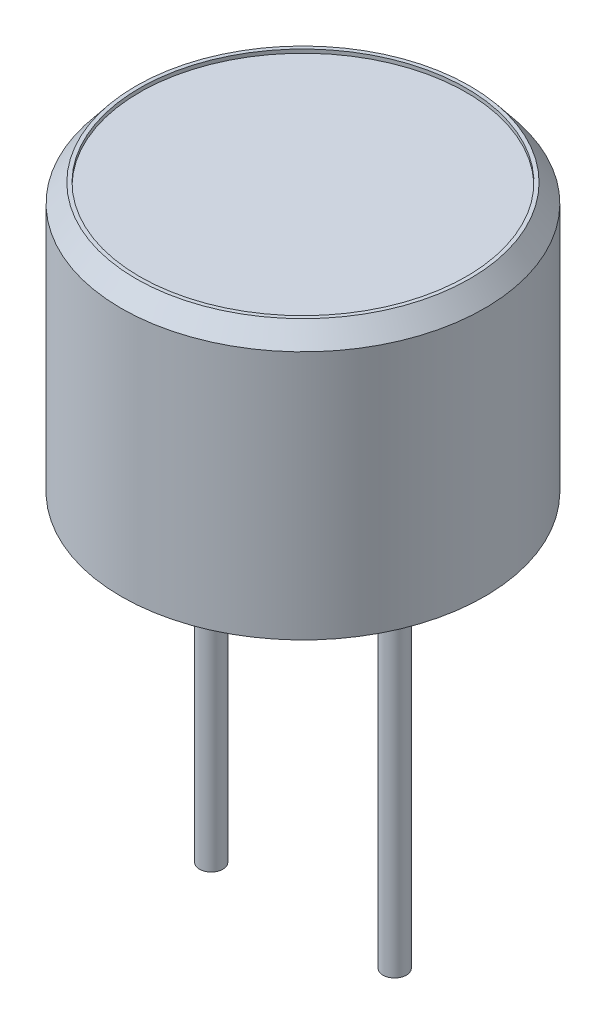
SolidWorks part; units mm, degrees
ref_plane "Front Plane" through (0, 0, 0) normal (0, 0, 1) x (1, 0, 0)
ref_plane "Top Plane" through (0, 0, 0) normal (0, 1, 0) x (1, 0, 0)
ref_plane "Right Plane" through (0, 0, 0) normal (1, 0, 0) x (0, 0, -1)
sketch "Sketch1" plane through (0, 0, 0) normal (0, 1, 0) x (1, 0, 0)
  circle A0 centre (0, 0) radius 4.95
  dimension "D1" = 9.9
extrude "Boss-Extrude1" add sketch "Sketch1" along normal blind 7.3
chamfer "Chamfer1" distance 0.5 distance2 0.4 1 edges at (0, 7.3, 4.95)
sketch "Sketch2" plane through (0, 0, 0) normal (0, -1, 0) x (1, 0, 0)
  line L0 (-2.5, 0) -> (2.5, 0) construction
  circle A0 centre (-2.5, 0) radius 0.32
  circle A1 centre (2.5, 0) radius 0.32
  point P4 (0, 0)
  dimension "D2" = 0.64
  dimension "D1" = 5
extrude "Boss-Extrude2" add sketch "Sketch2" along normal blind 10
sketch "Sketch3" plane through (0, 7.3, 0) normal (0, 1, 0) x (1, 0, 0)
  circle A0 centre (0, 0) radius 4.45
  circle A1 centre (0, 0) radius 4.55
  circle A2 centre (0, 0) radius 4.55
  dimension "D1" = 0
  dimension "D2" = 0.1
extrude "Cut-Extrude1" cut sketch "Sketch3" against normal blind 0.1 contours A0
